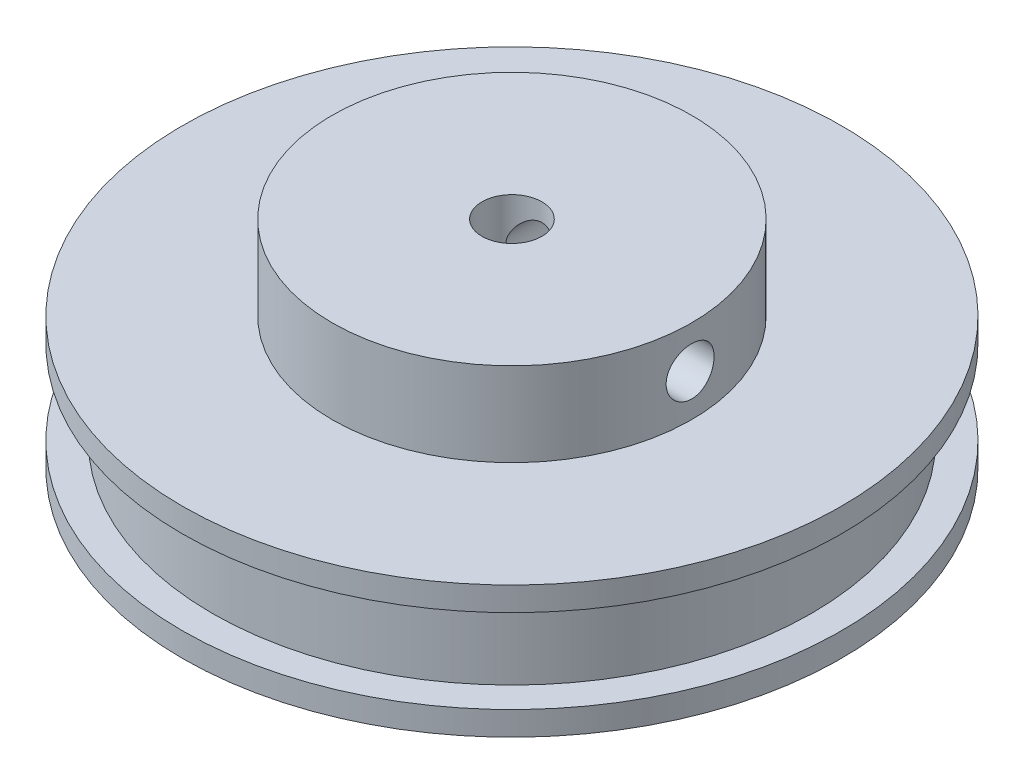
SolidWorks part; units mm, degrees
ref_plane "Front Plane" through (0, 0, 0) normal (0, 0, 1) x (1, 0, 0)
ref_plane "Top Plane" through (0, 0, 0) normal (0, 1, 0) x (1, 0, 0)
ref_plane "Right Plane" through (0, 0, 0) normal (1, 0, 0) x (0, 0, -1)
sketch "Sketch1" plane through (0, 0, 0) normal (0, 1, 0) x (1, 0, 0)
  circle A0 centre (0, 0) radius 27.5
  dimension "D1" = 55
extrude "Boss-Extrude1" add sketch "Sketch1" along normal blind 2
sketch "Sketch2" plane through (0, 2, 0) normal (0, 1, 0) x (1, 0, 0)
  circle A0 centre (0, 0) radius 25
  dimension "D1" = 50
extrude "Boss-Extrude2" add sketch "Sketch2" along normal blind 7
sketch "Sketch3" plane through (0, 9, 0) normal (0, 1, 0) x (1, 0, 0)
  circle A0 centre (0, 0) radius 27.5
  dimension "D1" = 55
extrude "Boss-Extrude3" add sketch "Sketch3" along normal blind 2
sketch "Sketch4" plane through (0, 11, 0) normal (0, 1, 0) x (1, 0, 0)
  circle A0 centre (0, 0) radius 15
  dimension "D1" = 30
extrude "Boss-Extrude4" add sketch "Sketch4" along normal blind 7
sketch "Sketch5" plane through (0, 18, 0) normal (0, 1, 0) x (1, 0, 0)
  circle A0 centre (0, 0) radius 2.5
  dimension "D1" = 5
extrude "Cut-Extrude1" cut sketch "Sketch5" against normal through all
sketch "Sketch6" plane through (0, 0, 0) normal (0, 0, 1) x (1, 0, 0)
  line L0 (15, 18) -> (-15, 18) construction
  circle A0 centre (0, 14.5) radius 2
  dimension "D1" = 4
  dimension "D2" = 3.5
extrude "Cut-Extrude2" cut sketch "Sketch6" against normal through all
pattern_circular "CirPattern1" count 2 every 90 about axis through (0, 18, 0) along (0, -1, 0) of "Cut-Extrude2"
